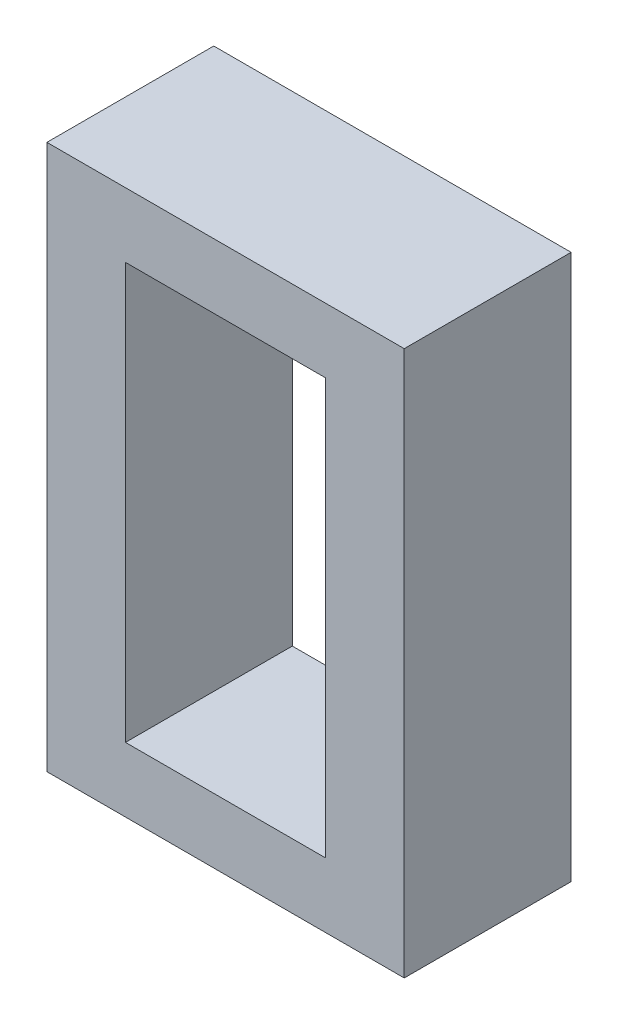
SolidWorks part; units mm, degrees
ref_plane "Front Plane" through (0, 0, 0) normal (0, 0, 1) x (1, 0, 0)
ref_plane "Top Plane" through (0, 0, 0) normal (0, 1, 0) x (1, 0, 0)
ref_plane "Right Plane" through (0, 0, 0) normal (1, 0, 0) x (0, 0, -1)
sketch "Sketch3" plane through (0, 0, 0) normal (0, 0, 1) x (1, 0, 0)
  line L1 (0, 0) -> (25.7, 0)
  line L2 (0, 0) -> (0, 39.2)
  line L3 (0, 39.2) -> (25.7, 39.2)
  line L4 (25.7, 0) -> (25.7, 39.2)
  line L5 (5.65, 4.65) -> (20.05, 4.65)
  line L6 (5.65, 4.65) -> (5.65, 34.55)
  line L7 (5.65, 34.55) -> (20.05, 34.55)
  line L8 (20.05, 4.65) -> (20.05, 34.55)
  point P9 (12.85, 34.55)
  point P10 (12.85, 39.2)
  point P11 (5.65, 19.6)
  point P12 (0, 19.6)
  dimension "D1" = 25.7
  dimension "D2" = 39.2
  dimension "D3" = 14.4
  dimension "D4" = 29.9
extrude "Boss-Extrude2" add sketch "Sketch3" along normal blind 12
